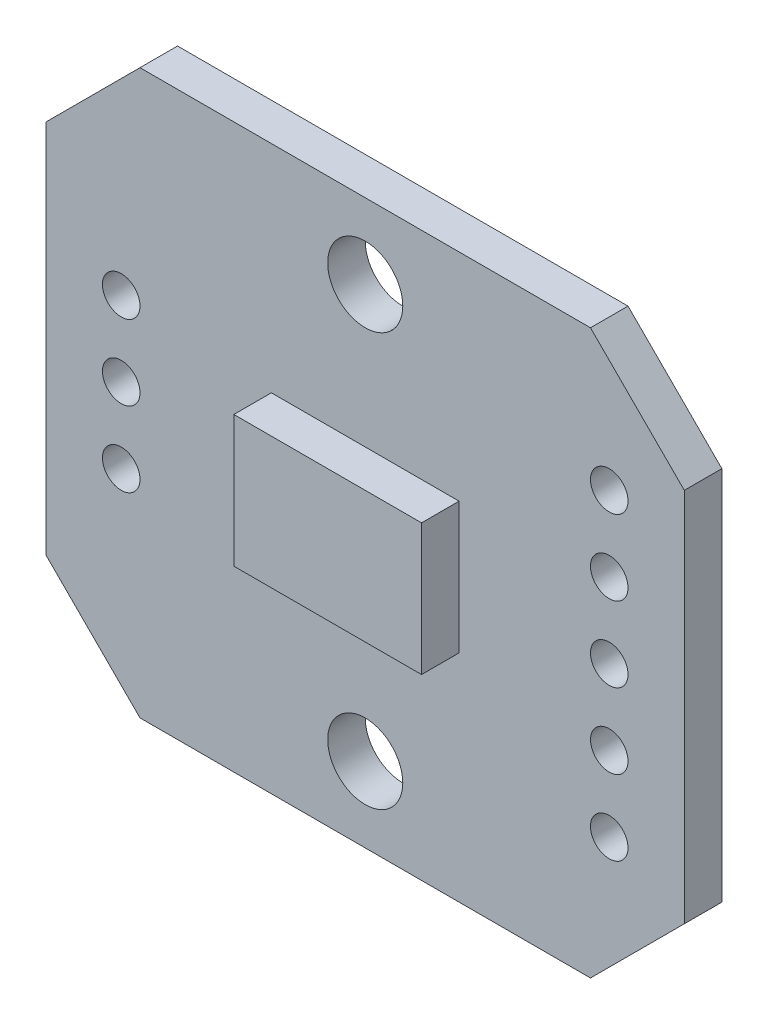
SolidWorks part; units mm, degrees
ref_plane "Front Plane" through (0, 0, 0) normal (0, 0, 1) x (1, 0, 0)
ref_plane "Top Plane" through (0, 0, 0) normal (0, 1, 0) x (1, 0, 0)
ref_plane "Right Plane" through (0, 0, 0) normal (1, 0, 0) x (0, 0, -1)
sketch "Sketch1" plane through (0, 0, 0) normal (0, 0, 1) x (1, 0, 0)
  line L1 (-8.5, -7.5) -> (8.5, -7.5)
  line L2 (-8.5, -7.5) -> (-8.5, 7.5)
  line L3 (-8.5, 7.5) -> (8.5, 7.5)
  line L4 (8.5, -7.5) -> (8.5, 7.5)
  line L5 (-8.5, -7.5) -> (8.5, 7.5) construction
  line L6 (-8.5, 7.5) -> (8.5, -7.5) construction
  point P0 (0, 0)
  dimension "D1" = 15
  dimension "D2" = 17
extrude "Boss-Extrude1" add sketch "Sketch1" along normal blind 1
chamfer "Chamfer1" distance 2.5 angle 45 4 edges at (-8.5, -7.5, 0.5) (8.5, -7.5, 0.5) (-8.5, 7.5, 0.5) (8.5, 7.5, 0.5)
sketch "Sketch2" plane through (0, 0, 0) normal (0, 0, 1) x (1, 0, 0)
  line L1 (-2.5, -1.75) -> (2.5, -1.75)
  line L2 (-2.5, -1.75) -> (-2.5, 1.75)
  line L3 (-2.5, 1.75) -> (2.5, 1.75)
  line L4 (2.5, -1.75) -> (2.5, 1.75)
  line L5 (-2.5, -1.75) -> (2.5, 1.75) construction
  line L6 (-2.5, 1.75) -> (2.5, -1.75) construction
  point P0 (0, 0)
  dimension "D1" = 5
  dimension "D2" = 3.5
extrude "Boss-Extrude2" add sketch "Sketch2" along normal blind 1 from surface at 1 starting at face at (0, 0, 1)
sketch "Sketch3" plane through (0, 0, 0) normal (0, 0, 1) x (1, 0, 0)
  line L0 (0, -5.5) -> (0, 5.5) construction
  line L1 (-6.5, 0) -> (6.5, 0) construction
  circle A0 centre (0, 5.5) radius 1
  circle A1 centre (0, -5.5) radius 1
  circle A2 centre (6.5, 0) radius 0.5
  circle A3 centre (-6.5, 0) radius 0.5
  circle A4 centre (6.5, 2) radius 0.5
  circle A5 centre (6.5, 4) radius 0.5
  circle A6 centre (-6.5, 2) radius 0.5
  circle A7 centre (-6.5, -2) radius 0.5
  circle A8 centre (6.5, -4) radius 0.5
  circle A9 centre (6.5, -2) radius 0.5
  point P4 (0, 0)
  point P10 (0, 0)
  dimension "D2" = 2
  dimension "D4" = 1
  dimension "D1" = 11
  dimension "D3" = 13
  dimension "D5" = 3
  dimension "D6" = 2
extrude "Cut-Extrude1" cut sketch "Sketch3" along normal blind 1
sketch "Sketch4" plane through (0, 0, 0) normal (0, 0, 1) x (1, 0, 0)
  line L1 (-1.6182, -3.1667) -> (0.3818, -3.1667)
  line L2 (-1.6182, -3.1667) -> (-1.6182, -1.9667)
  line L3 (-1.6182, -1.9667) -> (0.3818, -1.9667)
  line L4 (0.3818, -3.1667) -> (0.3818, -1.9667)
  line L5 (-1.6182, -3.1667) -> (0.3818, -1.9667) construction
  line L6 (-1.6182, -1.9667) -> (0.3818, -3.1667) construction
  line L7 (-2.6708, -5.4834) -> (-2.1708, -5.4834)
  line L8 (-2.6708, -5.4834) -> (-2.6708, -4.2834)
  line L9 (-2.6708, -4.2834) -> (-2.1708, -4.2834)
  line L10 (-2.1708, -5.4834) -> (-2.1708, -4.2834)
  line L11 (-2.6708, -5.4834) -> (-2.1708, -4.2834) construction
  line L12 (-2.6708, -4.2834) -> (-2.1708, -5.4834) construction
  line L13 (2.537, -5.2385) -> (4.037, -5.2385)
  line L14 (2.537, -5.2385) -> (2.537, -4.4385)
  line L15 (2.537, -4.4385) -> (4.037, -4.4385)
  line L16 (4.037, -5.2385) -> (4.037, -4.4385)
  line L17 (2.537, -5.2385) -> (4.037, -4.4385) construction
  line L18 (2.537, -4.4385) -> (4.037, -5.2385) construction
  point P0 (-0.6182, -2.5667)
  point P5 (-2.4208, -4.8834)
  point P10 (3.287, -4.8385)
  dimension "D1" = 1.2
  dimension "D2" = 2
  dimension "D3" = 1.2
  dimension "D4" = 0.5
  dimension "D5" = 0.8
  dimension "D6" = 1.5
extrude "Boss-Extrude3" add sketch "Sketch4" against normal blind 0.5 from surface at 0 starting at face at (7, 2, 0)
sketch "Sketch5" plane through (0, 0, 0) normal (0, 0, 1) x (1, 0, 0)
  line L1 (5, -3.25) -> (8, -3.25)
  line L2 (5, -3.25) -> (5, -4.75)
  line L3 (5, -4.75) -> (8, -4.75)
  line L4 (8, -3.25) -> (8, -4.75)
  line L5 (5, -3.25) -> (8, -4.75) construction
  line L6 (5, -4.75) -> (8, -3.25) construction
  line L7 (5, -1.25) -> (8, -1.25)
  line L8 (5, -1.25) -> (5, -2.75)
  line L9 (5, -2.75) -> (8, -2.75)
  line L10 (8, -1.25) -> (8, -2.75)
  line L11 (5, -1.25) -> (8, -2.75) construction
  line L12 (5, -2.75) -> (8, -1.25) construction
  line L13 (5, 0.75) -> (8, 0.75)
  line L14 (5, 0.75) -> (5, -0.75)
  line L15 (5, -0.75) -> (8, -0.75)
  line L16 (8, 0.75) -> (8, -0.75)
  line L17 (5, 0.75) -> (8, -0.75) construction
  line L18 (5, -0.75) -> (8, 0.75) construction
  line L19 (5, 2.75) -> (8, 2.75)
  line L20 (5, 2.75) -> (5, 1.25)
  line L21 (5, 1.25) -> (8, 1.25)
  line L22 (8, 2.75) -> (8, 1.25)
  line L23 (5, 2.75) -> (8, 1.25) construction
  line L24 (5, 1.25) -> (8, 2.75) construction
  line L25 (5, 4.75) -> (8, 4.75)
  line L26 (5, 4.75) -> (5, 3.25)
  line L27 (5, 3.25) -> (8, 3.25)
  line L28 (8, 4.75) -> (8, 3.25)
  line L29 (5, 4.75) -> (8, 3.25) construction
  line L30 (5, 3.25) -> (8, 4.75) construction
  line L31 (-8, -1.25) -> (-5, -1.25)
  line L32 (-8, -1.25) -> (-8, -2.75)
  line L33 (-8, -2.75) -> (-5, -2.75)
  line L34 (-5, -1.25) -> (-5, -2.75)
  line L35 (-8, -1.25) -> (-5, -2.75) construction
  line L36 (-8, -2.75) -> (-5, -1.25) construction
  line L37 (-8, 0.75) -> (-5, 0.75)
  line L38 (-8, 0.75) -> (-8, -0.75)
  line L39 (-8, -0.75) -> (-5, -0.75)
  line L40 (-5, 0.75) -> (-5, -0.75)
  line L41 (-8, 0.75) -> (-5, -0.75) construction
  line L42 (-8, -0.75) -> (-5, 0.75) construction
  line L43 (-8, 2.75) -> (-5, 2.75)
  line L44 (-8, 2.75) -> (-8, 1.25)
  line L45 (-8, 1.25) -> (-5, 1.25)
  line L46 (-5, 2.75) -> (-5, 1.25)
  line L47 (-8, 2.75) -> (-5, 1.25) construction
  line L48 (-8, 1.25) -> (-5, 2.75) construction
  point P0 (6.5, -4)
  point P6 (6.5, -2)
  point P12 (6.5, 0)
  point P18 (6.5, 2)
  point P24 (6.5, 4)
  point P30 (-6.5, -2)
  point P36 (-6.5, 0)
  point P42 (-6.5, 2)
  dimension "D1" = 3
  dimension "D2" = 1.5
extrude "Cut-Extrude2" cut sketch "Sketch5" along normal blind 0.01
